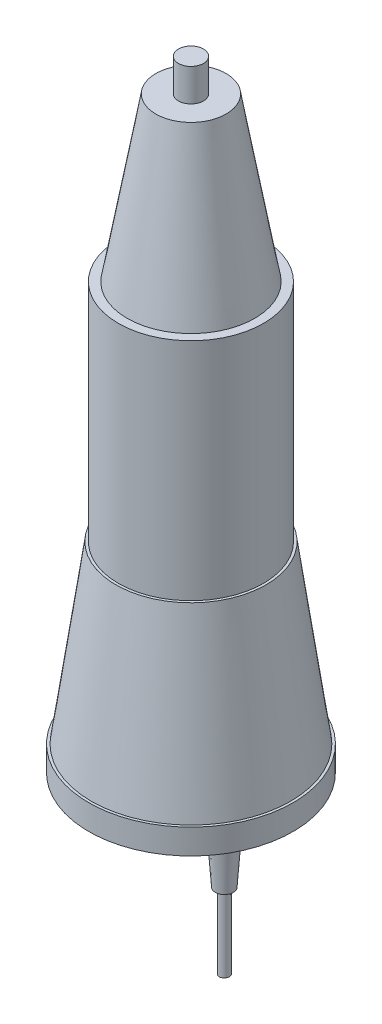
SolidWorks part; units mm, degrees
ref_plane "Plane1" through (0, 0, 0) normal (0, 0, 1) x (1, 0, 0)
ref_plane "Plane2" through (0, 0, 0) normal (0, 1, 0) x (1, 0, 0)
ref_plane "Plane3" through (0, 0, 0) normal (1, 0, 0) x (0, 0, -1)
sketch "Sketch1" plane through (0, 0, 0) normal (0, 1, 0) x (1, 0, 0)
  circle A0 centre (0, 0) radius 29
  dimension "D1" = 58
extrude "Boss-Extrude1" add sketch "Sketch1" along normal blind 90
sketch "Sketch2" plane through (0, 90, 0) normal (0, 1, 0) x (1, 0, 0)
  circle A1 centre (0, 0) radius 25.5
  dimension "D1" = 51
extrude "Boss-Extrude3" add sketch "Sketch2" along normal blind 65 draft 10
sketch "Sketch4" plane through (0, 155, 0) normal (0, 1, 0) x (1, 0, 0)
  circle A1 centre (0, 0) radius 5
  dimension "D1" = 10
extrude "Boss-Extrude4" add sketch "Sketch4" along normal blind 13
sketch "Sketch10" plane through (0, 0, 0) normal (0, -1, 0) x (1, 0, 0)
  circle A0 centre (0, 0) radius 30
  circle A1 centre (0, 0) radius 29 construction
  dimension "D1" = 1
extrude "Boss-Extrude5" add sketch "Sketch10" along normal blind 70 draft 8 draft outward yes
sketch "Sketch11" plane through (0, -70, 0) normal (0, -1, 0) x (1, 0, 0)
  circle A1 centre (0, 0) radius 40.8379
  circle A2 centre (0, 0) radius 39.8379 construction
  dimension "D1" = 1
extrude "Boss-Extrude6" add sketch "Sketch11" along normal blind 10
sketch "Sketch12" plane through (0, -80, 0) normal (0, -1, 0) x (1, 0, 0)
  circle A0 centre (26.3463, 13.0035) radius 5
  point P2 (-30.0866, -18.4676)
  point P3 (26.3463, 13.0035)
  dimension "D1" = 10
extrude "Boss-Extrude7" add sketch "Sketch12" along normal blind 20 draft 4
sketch "Sketch14" plane through (0, -100, 0) normal (0, -1, 0) x (1, 0, 0)
  circle A0 centre (26.3463, 13.0035) radius 2
  dimension "D1" = 4
extrude "Boss-Extrude8" add sketch "Sketch14" along normal blind 30
